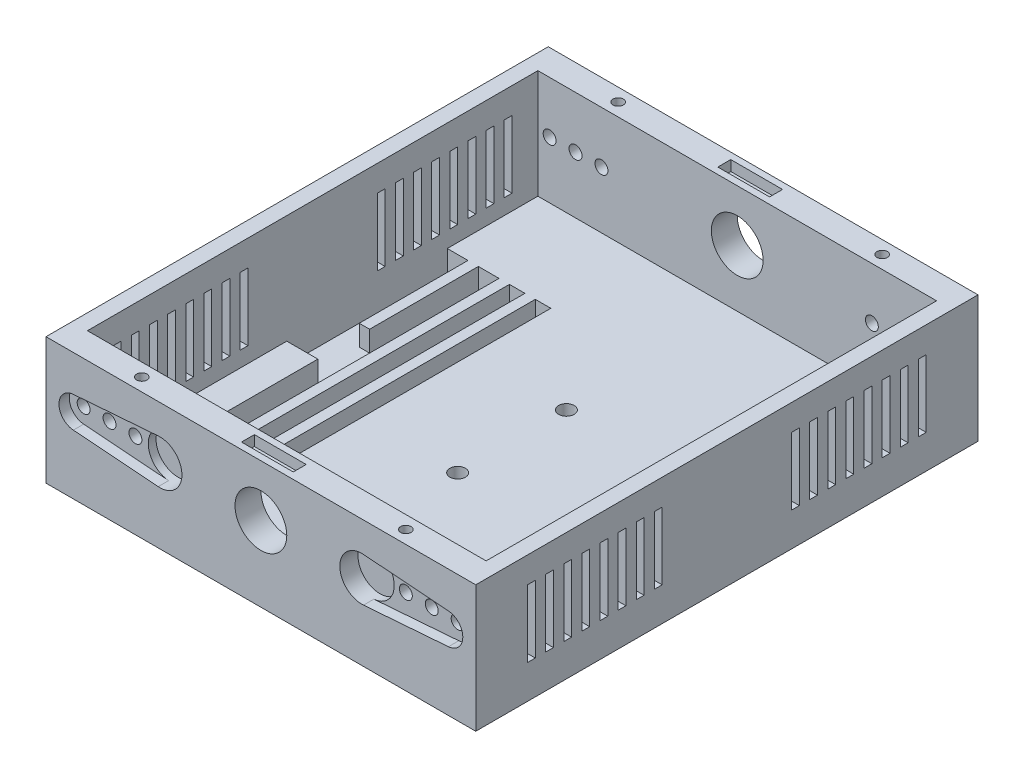
SolidWorks part; units mm, degrees
ref_plane "Front Plane" through (0, 0, 0) normal (0, 0, 1) x (1, 0, 0)
ref_plane "Top Plane" through (0, 0, 0) normal (0, 1, 0) x (1, 0, 0)
ref_plane "Right Plane" through (0, 0, 0) normal (1, 0, 0) x (0, 0, -1)
sketch "Sketch1" plane through (0, 0, 0) normal (0, 1, 0) x (1, 0, 0)
  line L1 (-45.3077, 72.9409) -> (37.6923, 72.9409)
  line L2 (-45.3077, 72.9409) -> (-45.3077, -24.0591)
  line L3 (-45.3077, -24.0591) -> (37.6923, -24.0591)
  line L4 (37.6923, 72.9409) -> (37.6923, -24.0591)
  line L5 (-45.3077, -24.0591) -> (-45.3077, 10.9409) construction
  line L6 (-45.3077, 72.9409) -> (-45.3077, 37.9409) construction
  line L7 (37.6923, 72.9409) -> (37.6923, 37.9409) construction
  line L8 (37.6923, -24.0591) -> (37.6923, 10.9409) construction
  dimension "D2" = 97
  dimension "D7" = 83
extrude "Boss-Extrude1" add sketch "Sketch1" along normal blind 6
sketch "Sketch2" plane through (0, 6, 0) normal (0, 1, 0) x (1, 0, 0)
  line L1 (-45.3077, 72.9409) -> (37.6923, 72.9409)
  line L2 (-45.3077, 72.9409) -> (-45.3077, -24.0591)
  line L3 (-45.3077, -24.0591) -> (37.6923, -24.0591)
  line L4 (37.6923, 72.9409) -> (37.6923, -24.0591)
  line L5 (-42.3077, 67.9409) -> (34.6923, 67.9409)
  line L6 (-42.3077, 67.9409) -> (-42.3077, -19.0591)
  line L7 (-42.3077, -19.0591) -> (34.6923, -19.0591)
  line L8 (34.6923, 67.9409) -> (34.6923, -19.0591)
  dimension "D1" = 5
  dimension "D2" = 5
  dimension "D3" = 3
  dimension "D4" = 3
  dimension "D5" = 87
  dimension "D6" = 77
extrude "Boss-Extrude2" add sketch "Sketch2" along normal blind 21
sketch "Sketch3" plane through (0, 0, 24.0591) normal (0, 0, 1) x (1, 0, 0)
  line L0 (-45.3077, 27) -> (37.6923, 27) construction
  line L2 (-23.3077, 17) -> (15.6923, 17) construction
  circle A2 centre (-23.3077, 17) radius 4.25
  circle A3 centre (15.6923, 17) radius 4.25
  dimension "D3" = 8.5
  dimension "D4" = 8.5
  dimension "D1" = 10
extrude "Cut-Extrude1" cut sketch "Sketch3" against normal blind 3.5
sketch "Sketch5" plane through (0, 0, 24.0591) normal (0, 0, 1) x (1, 0, 0)
  line L0 (-23.3077, 17) -> (15.6923, 17) construction
  line L1 (15.6923, 17) -> (32.1923, 17) construction
  line L2 (-23.3077, 17) -> (-39.8077, 17) construction
  line L3 (-40.035, 19.9914) -> (-23.6297, 21.2378)
  line L4 (-40.035, 14.0086) -> (-23.6297, 12.7622)
  line L5 (16.0143, 21.2378) -> (32.4196, 19.9914)
  line L6 (16.0143, 12.7622) -> (32.4196, 14.0086)
  arc A0 (-40.035, 19.9914) -> (-40.035, 14.0086) centre (-39.8077, 17) ccw
  arc A1 (32.4196, 14.0086) -> (32.4196, 19.9914) centre (32.1923, 17) ccw
  arc A2 (16.0143, 21.2378) -> (16.0143, 12.7622) centre (15.6923, 17) ccw
  arc A3 (-23.6297, 12.7622) -> (-23.6297, 21.2378) centre (-23.3077, 17) ccw
  dimension "D3" = 6
  dimension "D4" = 6
  dimension "D1" = 16.5
  dimension "D2" = 16.5
extrude "Cut-Extrude2" cut sketch "Sketch5" against normal blind 2
sketch "Sketch6" plane through (0, 0, 24.0591) normal (0, 0, 1) x (1, 0, 0)
  line L0 (-23.5376, 17) -> (-30.0376, 17) construction
  line L1 (-30.0376, 17) -> (-35.0376, 17) construction
  line L2 (15.6923, 17) -> (22.1923, 17) construction
  line L3 (22.1923, 17) -> (27.1923, 17) construction
  line L4 (-35.0376, 17) -> (-40.0376, 17) construction
  line L5 (27.1923, 17) -> (32.1923, 17) construction
  circle A0 centre (-35.0376, 17) radius 1.25
  circle A1 centre (-30.0376, 17) radius 1.25
  circle A2 centre (22.1923, 17) radius 1.25
  circle A3 centre (27.1923, 17) radius 1.25
  circle A4 centre (32.1923, 17) radius 1.25
  circle A5 centre (-40.0376, 17) radius 1.25
  dimension "D5" = 2.5
  dimension "D1" = 6.5
  dimension "D2" = 5
  dimension "D3" = 6.5
  dimension "D4" = 5
  dimension "D6" = 5
  dimension "D7" = 5
extrude "Cut-Extrude4" cut sketch "Sketch6" against normal blind 5
sketch "Sketch8" plane through (0, 27, 0) normal (0, 1, 0) x (1, 0, 0)
  line L0 (-45.3077, 24.4409) -> (-45.3077, 16.4533)
  line L1 (-45.3077, 72.9409) -> (-45.3077, -24.0591) construction
ref_plane "Plane1" through (-45.3077, 27, -24.4409) normal (0, 0, 1) x (1, 0, 0)
mirror "Mirror1" about plane through (-45.3077, 27, -24.4409) normal (0, 0, 1) of "Cut-Extrude4", "Cut-Extrude1", "Cut-Extrude2"
sketch "Sketch10" plane through (0, 6, 0) normal (0, 1, 0) x (1, 0, 0)
  line L0 (-42.3077, 24.4409) -> (34.6923, 24.4409) construction
  line L1 (-42.3077, 67.9409) -> (-42.3077, -19.0591) construction
  line L2 (34.6923, -19.0591) -> (34.6923, 67.9409) construction
  line L3 (-3.8077, 34.9409) -> (-3.8077, 24.4409) construction
  line L4 (-3.8077, 24.4409) -> (-3.8077, 13.9409) construction
  circle A0 centre (-3.8077, 34.9409) radius 1.5
  circle A1 centre (-3.8077, 13.9409) radius 1.5
  dimension "D3" = 3
  dimension "D4" = 3
  dimension "D1" = 10.5
  dimension "D2" = 10.5
extrude "Cut-Extrude5" cut sketch "Sketch10" against normal blind 10
sketch "Sketch11" plane through (0, 6, 0) normal (0, 1, 0) x (1, 0, 0)
  line L0 (34.6923, 24.4409) -> (-42.3077, 24.4409) construction
  line L1 (34.6923, -19.0591) -> (34.6923, 67.9409) construction
  line L2 (-42.3077, 67.9409) -> (-42.3077, -19.0591) construction
  line L3 (-36.3077, 19.4409) -> (-36.3077, -1.5591)
  line L4 (-38.3077, 29.4409) -> (-36.3077, 29.4409)
  line L5 (-42.3077, 26.9409) -> (-42.3077, 19.4409)
  line L6 (-42.3077, 19.4409) -> (-36.3077, 19.4409)
  line L10 (-32.3077, -1.5591) -> (-36.3077, -1.5591)
  line L14 (-32.3077, 50.4409) -> (-36.3077, 50.4409)
  line L15 (-36.3077, 29.4409) -> (-36.3077, 50.4409)
  line L16 (-32.3077, 50.4409) -> (-30.3077, 50.4409) construction
  line L17 (-30.3077, 50.4409) -> (-27.3077, 50.4409) construction
  line L18 (-27.3077, 50.4409) -> (-25.3077, 50.4409) construction
  line L19 (-25.3077, 50.4409) -> (-22.3077, 50.4409) construction
  line L20 (-32.3077, 50.4409) -> (-32.3077, -1.5591)
  line L21 (-42.3077, 67.9409) -> (-42.3077, -19.0591) construction
  line L22 (-30.3077, 50.4409) -> (-27.3077, 50.4409)
  line L23 (-30.3077, 50.4409) -> (-30.3077, -1.5591)
  line L24 (-30.3077, -1.5591) -> (-27.3077, -1.5591)
  line L25 (-27.3077, 50.4409) -> (-27.3077, -1.5591)
  line L26 (-25.3077, 50.4409) -> (-22.3077, 50.4409)
  line L27 (-25.3077, 50.4409) -> (-25.3077, -1.5591)
  line L28 (-25.3077, -1.5591) -> (-22.3077, -1.5591)
  line L29 (-22.3077, 50.4409) -> (-22.3077, -1.5591)
  line L30 (-42.3077, 50.4409) -> (-38.3077, 50.4409)
  line L31 (-42.3077, 50.4409) -> (-42.3077, 26.9409)
  line L33 (-38.3077, 50.4409) -> (-38.3077, 29.4409)
  circle A0 centre (-42.3077, 24.4409) radius 2.5 construction
  dimension "D1" = 5
  dimension "D2" = 20
  dimension "D3" = 4
  dimension "D4" = 26
  dimension "D5" = 4
  dimension "D6" = 26
  dimension "D7" = 2
  dimension "D8" = 3
  dimension "D9" = 2
  dimension "D10" = 3
  dimension "D11" = 5
  dimension "D12" = 6
  dimension "D13" = 5
extrude "Cut-Extrude6" cut sketch "Sketch11" against normal blind 4
sketch "Sketch12" plane through (0, 27, 0) normal (0, 1, 0) x (1, 0, 0)
  line L0 (-3.8077, 67.9409) -> (-3.8077, 72.9409) construction
  line L1 (34.6923, 67.9409) -> (-42.3077, 67.9409) construction
  line L2 (37.6923, 72.9409) -> (-45.3077, 72.9409) construction
  line L3 (-8.8077, 70.4409) -> (-3.8077, 70.4409) construction
  line L4 (-3.8077, -24.0591) -> (-3.8077, -19.0591) construction
  line L5 (-45.3077, -24.0591) -> (37.6923, -24.0591) construction
  line L6 (-42.3077, -19.0591) -> (34.6923, -19.0591) construction
  line L7 (-3.8077, -21.5591) -> (-8.8077, -21.5591) construction
  line L9 (-8.8077, -20.3091) -> (1.1923, -20.3091)
  line L10 (-8.8077, -20.3091) -> (-8.8077, -22.8091)
  line L11 (-8.8077, -22.8091) -> (1.1923, -22.8091)
  line L12 (1.1923, -20.3091) -> (1.1923, -22.8091)
  line L13 (-8.8077, 71.6909) -> (1.1923, 71.6909)
  line L14 (-8.8077, 71.6909) -> (-8.8077, 69.1909)
  line L15 (-8.8077, 69.1909) -> (1.1923, 69.1909)
  line L16 (1.1923, 71.6909) -> (1.1923, 69.1909)
  circle A0 centre (-8.8077, -21.5591) radius 1.25 construction
  circle A1 centre (-8.8077, 70.4409) radius 1.25 construction
  dimension "D3" = 2.5
  dimension "D4" = 2.5
  dimension "D1" = 5
  dimension "D2" = 5
  dimension "D5" = 10
  dimension "D6" = 10
  dimension "D7" = 2.5
  dimension "D8" = 2.5
extrude "Cut-Extrude7" cut sketch "Sketch12" against normal blind 2
sketch "Sketch13" plane through (0, 27, 0) normal (0, 1, 0) x (1, 0, 0)
  line L0 (-3.8077, 70.4409) -> (21.6923, 70.4409) construction
  line L1 (-3.8077, 70.4409) -> (-29.3077, 70.4409) construction
  line L2 (-3.8077, -21.5591) -> (21.6923, -21.5591) construction
  line L3 (-3.8077, -21.5591) -> (-29.3077, -21.5591) construction
  line L4 (-29.3077, 70.4409) -> (-45.3077, 70.4409) construction
  line L5 (-45.3077, 72.9409) -> (-45.3077, -24.0591) construction
  line L6 (-29.3077, -21.5591) -> (-45.3077, -21.5591) construction
  circle A0 centre (-29.3077, 70.4409) radius 1
  circle A1 centre (21.6923, 70.4409) radius 1
  circle A2 centre (-29.3077, -21.5591) radius 1
  circle A3 centre (21.6923, -21.5591) radius 1
  dimension "D4" = 2
  dimension "D1" = 16
  dimension "D2" = 25.5
  dimension "D3" = 16
extrude "Cut-Extrude8" cut sketch "Sketch13" against normal blind 5
sketch "Sketch15" plane through (-45.3077, 0, 0) normal (-1, 0, 0) x (0, 0, 1)
  line L0 (-72.9409, 27) -> (-67.9409, 27)
  line L1 (-72.9409, 27) -> (24.0591, 27) construction
  line L2 (-72.9409, 27) -> (-72.9409, 0) construction
  line L3 (-67.9409, 27) -> (19.0591, 27) construction
  line L5 (-67.9409, 9) -> (19.0591, 9) construction
  line L6 (19.0591, 27) -> (19.0591, 9) construction
  line L7 (-72.9409, 0) -> (24.0591, 0) construction
  line L8 (24.0591, 27) -> (24.0591, 0) construction
  line L9 (-67.9409, 27) -> (-67.9409, 22) construction
  line L10 (-67.9409, 22) -> (-67.9409, 14) construction
  line L11 (-67.9409, 14) -> (-67.9409, 9) construction
  line L12 (-67.9409, 22) -> (-62.9409, 22) construction
  line L13 (-62.9409, 22) -> (-61.4409, 22) construction
  line L14 (-61.4409, 22) -> (-59.4409, 22) construction
  line L15 (-59.4409, 22) -> (-57.9409, 22) construction
  line L16 (-57.9409, 22) -> (-55.9409, 22) construction
  line L17 (-55.9409, 22) -> (-54.4409, 22) construction
  line L18 (-54.4409, 22) -> (-52.4409, 22) construction
  line L19 (-52.4409, 22) -> (-50.9409, 22) construction
  line L20 (-50.9409, 22) -> (-48.9409, 22) construction
  line L21 (-48.9409, 22) -> (-47.4409, 22) construction
  line L22 (-47.4409, 22) -> (-45.4409, 22) construction
  line L23 (-45.4409, 22) -> (-43.9409, 22) construction
  line L24 (-43.9409, 22) -> (-41.9409, 22) construction
  line L25 (-41.9409, 22) -> (-40.4409, 22) construction
  line L26 (-40.4409, 22) -> (-38.4409, 22) construction
  line L27 (-38.4409, 22) -> (-36.9409, 22) construction
  line L28 (-36.9409, 22) -> (-12.6545, 22) construction
  line L29 (-12.6545, 22) -> (-11.8789, 22) construction
  line L30 (-11.8789, 22) -> (-9.834, 22) construction
  line L31 (-9.834, 22) -> (-8.8469, 22) construction
  line L32 (-8.8469, 22) -> (-6.2027, 22) construction
  line L33 (-6.2027, 22) -> (-5.286, 22) construction
  line L34 (-5.286, 22) -> (-3.2412, 22) construction
  line L35 (-3.2412, 22) -> (-2.4303, 22) construction
  line L36 (-2.4303, 22) -> (0.2492, 22) construction
  line L37 (0.2492, 22) -> (1.2716, 22) construction
  line L38 (1.2716, 22) -> (4.1626, 22) construction
  line L39 (4.1626, 22) -> (4.7972, 22) construction
  line L40 (4.7972, 22) -> (6.4895, 22) construction
  line L41 (6.4895, 22) -> (7.6177, 22) construction
  line L42 (7.6177, 22) -> (8.9574, 22) construction
  line L43 (8.9574, 22) -> (9.7683, 22) construction
  line L44 (9.7683, 22) -> (19.0591, 22) construction
  line L46 (-62.9409, 22) -> (-61.4409, 22)
  line L47 (-62.9409, 22) -> (-62.9409, 9)
  line L48 (-62.9409, 9) -> (-61.4409, 9)
  line L49 (-61.4409, 22) -> (-61.4409, 9)
  line L50 (-59.4409, 22) -> (-57.9409, 22)
  line L51 (-59.4409, 22) -> (-59.4409, 9)
  line L52 (-59.4409, 9) -> (-57.9409, 9)
  line L53 (-57.9409, 22) -> (-57.9409, 9)
  line L54 (-55.9409, 22) -> (-54.4409, 22)
  line L55 (-55.9409, 22) -> (-55.9409, 9)
  line L56 (-55.9409, 9) -> (-54.4409, 9)
  line L57 (-54.4409, 22) -> (-54.4409, 9)
  line L58 (-52.4409, 22) -> (-50.9409, 22)
  line L59 (-52.4409, 22) -> (-52.4409, 9)
  line L60 (-52.4409, 9) -> (-50.9409, 9)
  line L61 (-50.9409, 22) -> (-50.9409, 9)
  line L62 (-48.9409, 22) -> (-47.4409, 22)
  line L63 (-48.9409, 22) -> (-48.9409, 9)
  line L64 (-48.9409, 9) -> (-47.4409, 9)
  line L65 (-47.4409, 22) -> (-47.4409, 9)
  line L66 (-45.4409, 22) -> (-43.9409, 22)
  line L67 (-45.4409, 22) -> (-45.4409, 9)
  line L68 (-45.4409, 9) -> (-43.9409, 9)
  line L69 (-43.9409, 22) -> (-43.9409, 9)
  line L70 (-41.9409, 22) -> (-40.4409, 22)
  line L71 (-41.9409, 22) -> (-41.9409, 9)
  line L72 (-41.9409, 9) -> (-40.4409, 9)
  line L73 (-40.4409, 22) -> (-40.4409, 9)
  line L74 (-38.4409, 22) -> (-36.9409, 22)
  line L75 (-38.4409, 22) -> (-38.4409, 9)
  line L76 (-38.4409, 9) -> (-36.9409, 9)
  line L77 (-36.9409, 22) -> (-36.9409, 9)
  dimension "D1" = 5
  dimension "D2" = 9
  dimension "D3" = 5
  dimension "D5" = 5
  dimension "D6" = 1.5
  dimension "D7" = 5
  dimension "D8" = 2
  dimension "D9" = 1.5
  dimension "D10" = 2
  dimension "D11" = 1.5
  dimension "D12" = 2
  dimension "D13" = 1.5
  dimension "D14" = 2
  dimension "D15" = 1.5
  dimension "D16" = 2
  dimension "D17" = 1.5
  dimension "D18" = 2
  dimension "D19" = 1.5
  dimension "D20" = 2
  dimension "D21" = 1.5
extrude "Cut-Extrude9" cut sketch "Sketch15" against normal blind 101 contours L49 L46 L47 L48 | L53 L50 L51 L52 | L57 L54 L55 L56 | L61 L58 L59 L60 | L65 L62 L63 L64 | L69 L66 L67 L68 | L73 L70 L71 L72 | L77 L74 L75 L76
mirror "Mirror2" about plane through (-45.3077, 27, -24.4409) normal (0, 0, 1) of "Cut-Extrude9"
chamfer "Chamfer2" distance 2.5 angle 45 4 edges at (37.6923, 0, -24.4409) (-3.8077, 0, 24.0591) (-45.3077, 0, -24.4409) (-3.8077, 0, -72.9409)
sketch "Sketch17" plane through (0, 0, 24.0591) normal (0, 0, 1) x (1, 0, 0)
  line L0 (-3.8077, 27) -> (-3.8077, 17) construction
  line L1 (-45.3077, 27) -> (37.6923, 27) construction
  circle A0 centre (-3.8077, 17) radius 5
  dimension "D1" = 10
  dimension "D2" = 10
extrude "Cut-Extrude10" cut sketch "Sketch17" against normal blind 105
sketch "Sketch19" plane through (0, 6, 0) normal (0, 1, 0) x (1, 0, 0)
  line L0 (34.6923, -19.0591) -> (16.6923, -19.0591) construction
  line L2 (34.6923, -19.0591) -> (24.6923, -19.0591) construction
  line L3 (-42.3077, -19.0591) -> (34.6923, -19.0591) construction
  line L4 (24.6923, -19.0591) -> (24.6923, -8.0591) construction
  line L5 (-42.3077, -19.0591) -> (34.6923, -19.0591) construction
  line L6 (16.6923, -19.0591) -> (16.6923, -2.0591) construction
  line L7 (34.6923, 67.9409) -> (34.6923, 62.9409) construction
  line L8 (16.6923, -2.0591) -> (24.6923, -2.0591)
  line L9 (16.6923, -2.0591) -> (16.6923, -8.0591)
  line L10 (16.6923, -8.0591) -> (24.6923, -8.0591)
  line L11 (24.6923, -2.0591) -> (24.6923, -8.0591)
  line L12 (34.6923, -19.0591) -> (34.6923, 67.9409) construction
  line L13 (34.6923, 62.9409) -> (24.6923, 62.9409) construction
  line L14 (34.6923, 67.9409) -> (34.6923, 56.9409) construction
  line L15 (34.6923, -19.0591) -> (34.6923, 67.9409) construction
  line L16 (34.6923, 56.9409) -> (16.6923, 56.9409) construction
  line L18 (24.6923, 62.9409) -> (16.6923, 62.9409)
  line L19 (24.6923, 62.9409) -> (24.6923, 56.9409)
  line L20 (24.6923, 56.9409) -> (16.6923, 56.9409)
  line L21 (16.6923, 62.9409) -> (16.6923, 56.9409)
  dimension "D1" = 10
  dimension "D2" = 11
  dimension "D3" = 18
  dimension "D4" = 17
  dimension "D5" = 5
  dimension "D6" = 10
  dimension "D7" = 18
  dimension "D8" = 11
extrude "Cut-Extrude11" cut sketch "Sketch19" against normal blind 10
